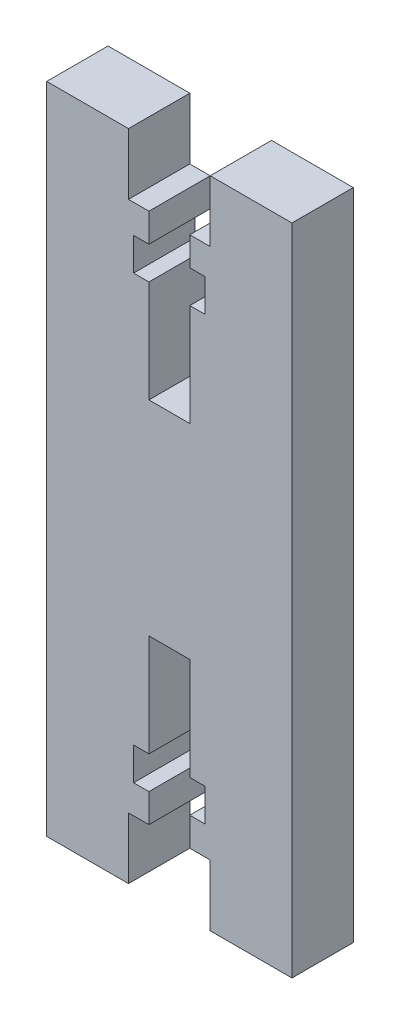
SolidWorks part; units mm, degrees
ref_plane "Plan de face" through (0, 0, 0) normal (0, 0, 1) x (1, 0, 0)
ref_plane "Plan de dessus" through (0, 0, 0) normal (0, 1, 0) x (1, 0, 0)
ref_plane "Plan de droite" through (0, 0, 0) normal (1, 0, 0) x (0, 0, -1)
sketch "Esquisse1" plane through (0, 0, 0) normal (0, 0, 1) x (1, 0, 0)
  line L0 (8, 0) -> (8, 6)
  line L1 (0, 0) -> (8, 0)
  line L2 (0, 0) -> (0, 64)
  line L3 (0, 32) -> (24, 32) construction
  line L4 (24, 0) -> (24, 64)
  line L5 (8, 6) -> (10, 6)
  line L6 (16, 6) -> (16, 0)
  line L7 (12, 0) -> (12, 32) construction
  line L8 (16, 0) -> (24, 0)
  line L9 (10, 6) -> (10, 8.8)
  line L10 (10, 8.8) -> (8.5, 8.8)
  line L11 (8.5, 8.8) -> (8.5, 12)
  line L12 (8.5, 12) -> (10, 12)
  line L13 (15.5, 12) -> (15.5, 8.8)
  line L14 (15.5, 8.8) -> (14, 8.8)
  line L15 (14, 8.8) -> (14, 6)
  line L16 (14, 6) -> (16, 6)
  line L17 (10, 12) -> (10, 22)
  line L18 (10, 22) -> (14, 22)
  line L19 (14, 22) -> (14, 12)
  line L20 (14, 12) -> (15.5, 12)
  line L21 (14, 52) -> (15.5, 52)
  line L22 (14, 42) -> (14, 52)
  line L23 (10, 42) -> (14, 42)
  line L24 (10, 52) -> (10, 42)
  line L25 (14, 58) -> (16, 58)
  line L26 (14, 55.2) -> (14, 58)
  line L27 (15.5, 55.2) -> (14, 55.2)
  line L28 (15.5, 52) -> (15.5, 55.2)
  line L29 (8.5, 52) -> (10, 52)
  line L30 (8.5, 55.2) -> (8.5, 52)
  line L31 (10, 55.2) -> (8.5, 55.2)
  line L32 (10, 58) -> (10, 55.2)
  line L33 (16, 64) -> (24, 64)
  line L34 (16, 58) -> (16, 64)
  line L35 (8, 58) -> (10, 58)
  line L36 (0, 64) -> (8, 64)
  line L37 (8, 64) -> (8, 58)
  dimension "D1" = 24
  dimension "D2" = 8
  dimension "D3" = 8
  dimension "D4" = 6
  dimension "D5" = 4
  dimension "D6" = 2
  dimension "D7" = 7
  dimension "D8" = 3.5
  dimension "D9" = 3.2
  dimension "D10" = 22
  dimension "D11" = 32
  dimension "D12" = 10
extrude "Boss.-Extru.1" add sketch "Esquisse1" along normal blind 6
equation "\"D6@Esquisse1\"=\"D5@Esquisse1\"/2"
equation "\"D8@Esquisse1\"=\"D7@Esquisse1\"/2"
